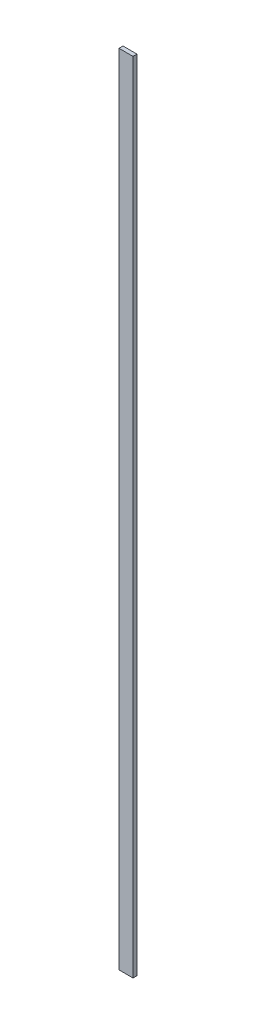
SolidWorks part; units mm, degrees
ref_plane "Plan de face" through (0, 0, 0) normal (0, 0, 1) x (1, 0, 0)
ref_plane "Plan de dessus" through (0, 0, 0) normal (0, 1, 0) x (1, 0, 0)
ref_plane "Plan de droite" through (0, 0, 0) normal (1, 0, 0) x (0, 0, -1)
sketch "Esquisse1" plane through (0, 0, 0) normal (0, 0, 1) x (1, 0, 0)
  line L1 (-21.7388, 33.9182) -> (-14.7388, 33.9182)
  line L2 (-21.7388, 33.9182) -> (-21.7388, -366.0818)
  line L3 (-21.7388, -366.0818) -> (-14.7388, -366.0818)
  line L4 (-14.7388, 33.9182) -> (-14.7388, -366.0818)
  dimension "D1" = 7
  dimension "D2" = 400
extrude "Boss.-Extru.1" add sketch "Esquisse1" along normal blind 2
